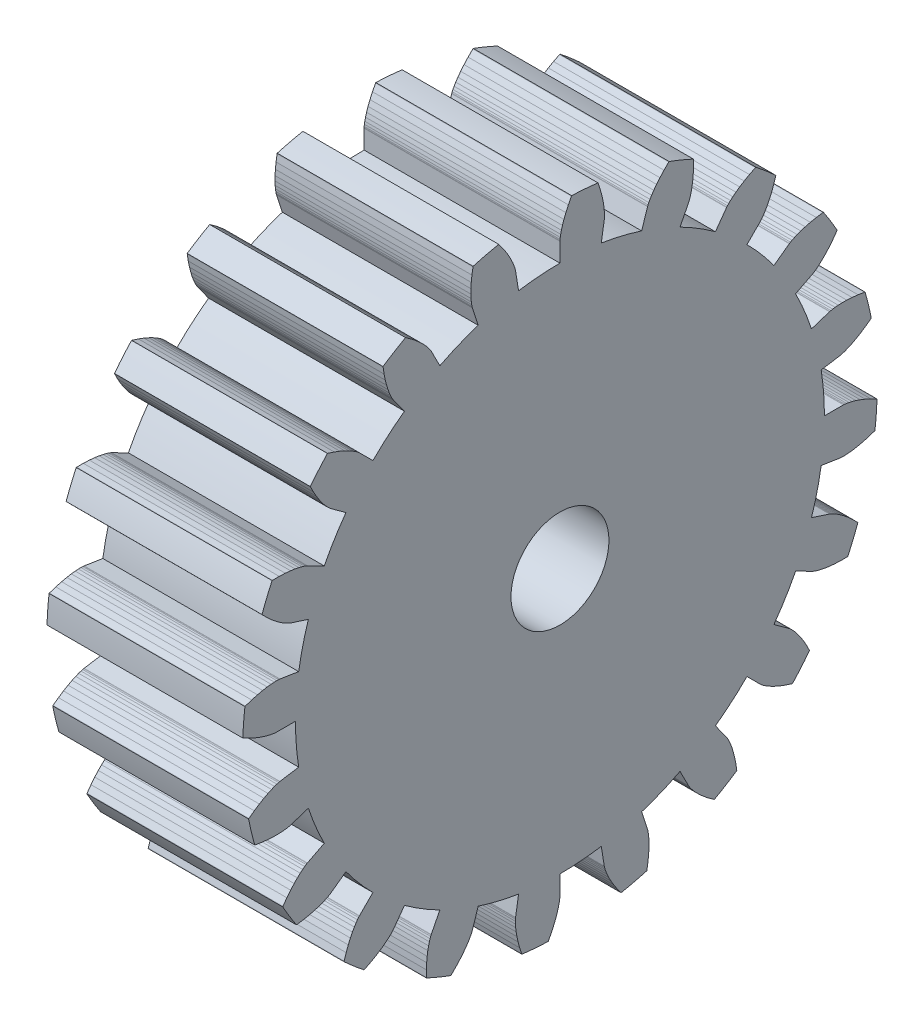
SolidWorks part; units mm, degrees
ref_plane "Front Plane" through (0, 0, 0) normal (0, 0, 1) x (1, 0, 0)
ref_plane "Top Plane" through (0, 0, 0) normal (0, 1, 0) x (1, 0, 0)
ref_plane "Right Plane" through (0, 0, 0) normal (1, 0, 0) x (0, 0, -1)
ref_plane "Plane1" through (12.7, 0, 0) normal (1, 0, 0) x (0, 0, -1)
sketch "Sketch1" plane through (12.7, 0, 0) normal (1, 0, 0) x (0, 0, -1)
  line L0 (2.6828, 16.9386) -> (2.8755, 18.1554)
  line L1 (2.8755, 18.1554) -> (2.8784, 18.1782)
  line L2 (2.8784, 18.1782) -> (2.8838, 18.2469)
  line L3 (2.8838, 18.2469) -> (2.8873, 18.3618)
  line L4 (2.8873, 18.3618) -> (2.8843, 18.5225)
  line L5 (2.8843, 18.5225) -> (2.87, 18.7288)
  line L6 (2.87, 18.7288) -> (2.8401, 18.9798)
  line L7 (2.8401, 18.9798) -> (2.79, 19.2742)
  line L8 (2.79, 19.2742) -> (2.7153, 19.6106)
  line L9 (2.7153, 19.6106) -> (2.6117, 19.9872)
  line L10 (2.6117, 19.9872) -> (2.4751, 20.4018)
  line L11 (2.4751, 20.4018) -> (2.4659, 20.4257)
  line L12 (0.7598, 20.56) -> (0.7469, 20.5378)
  line L13 (0.7469, 20.5378) -> (0.5471, 20.1497)
  line L14 (0.5471, 20.1497) -> (0.3859, 19.794)
  line L15 (0.3859, 19.794) -> (0.2595, 19.4734)
  line L16 (0.2595, 19.4734) -> (0.164, 19.1904)
  line L17 (0.164, 19.1904) -> (0.0951, 18.9472)
  line L18 (0.0951, 18.9472) -> (0.0488, 18.7457)
  line L19 (0.0488, 18.7457) -> (0.0206, 18.5874)
  line L20 (0.0206, 18.5874) -> (0.0061, 18.4734)
  line L21 (0.0061, 18.4734) -> (0.0008, 18.4047)
  line L22 (0.0008, 18.4047) -> (0, 18.3817)
  line L23 (0, 18.3817) -> (0, 17.1498)
  line L24 (-2.6828, 16.9386) -> (-2.8755, 18.1554)
  line L25 (-2.8755, 18.1554) -> (-2.8799, 18.178)
  line L26 (-2.8799, 18.178) -> (-2.8959, 18.245)
  line L27 (-2.8959, 18.245) -> (-2.9281, 18.3553)
  line L28 (-2.9281, 18.3553) -> (-2.9807, 18.5073)
  line L29 (-2.9807, 18.5073) -> (-3.058, 18.6991)
  line L30 (-3.058, 18.6991) -> (-3.164, 18.9285)
  line L31 (-3.164, 18.9285) -> (-3.3026, 19.193)
  line L32 (-3.3026, 19.193) -> (-3.4776, 19.4899)
  line L33 (-3.4776, 19.4899) -> (-3.6925, 19.8161)
  line L34 (-3.6925, 19.8161) -> (-3.9506, 20.1681)
  line L35 (-3.9506, 20.1681) -> (-3.9667, 20.188)
  line L36 (-5.6308, 19.7885) -> (-5.6362, 19.7634)
  line L37 (-5.6362, 19.7634) -> (-5.7063, 19.3326)
  line L38 (-5.7063, 19.3326) -> (-5.7497, 18.9444)
  line L39 (-5.7497, 18.9444) -> (-5.7708, 18.6005)
  line L40 (-5.7708, 18.6005) -> (-5.7742, 18.3018)
  line L41 (-5.7742, 18.3018) -> (-5.7645, 18.0493)
  line L42 (-5.7645, 18.0493) -> (-5.7463, 17.8433)
  line L43 (-5.7463, 17.8433) -> (-5.7242, 17.684)
  line L44 (-5.7242, 17.684) -> (-5.7028, 17.5712)
  line L45 (-5.7028, 17.5712) -> (-5.6866, 17.5041)
  line L46 (-5.6866, 17.5041) -> (-5.6803, 17.4821)
  line L47 (-5.6803, 17.4821) -> (-5.2996, 16.3104)
  line L48 (-7.7858, 15.2806) -> (-8.3451, 16.3782)
  line L49 (-8.3451, 16.3782) -> (-8.3562, 16.3984)
  line L50 (-8.3562, 16.3984) -> (-8.3922, 16.4572)
  line L51 (-8.3922, 16.4572) -> (-8.4569, 16.5521)
  line L52 (-8.4569, 16.5521) -> (-8.5539, 16.6804)
  line L53 (-8.5539, 16.6804) -> (-8.6866, 16.8389)
  line L54 (-8.6866, 16.8389) -> (-8.8583, 17.0243)
  line L55 (-8.8583, 17.0243) -> (-9.0719, 17.2331)
  line L56 (-9.0719, 17.2331) -> (-9.3301, 17.4614)
  line L57 (-9.3301, 17.4614) -> (-9.6353, 17.7051)
  line L58 (-9.6353, 17.7051) -> (-9.9895, 17.9602)
  line L59 (-9.9895, 17.9602) -> (-10.011, 17.9741)
  line L60 (-11.4702, 17.0799) -> (-11.4676, 17.0545)
  line L61 (-11.4676, 17.0545) -> (-11.4011, 16.6231)
  line L62 (-11.4011, 16.6231) -> (-11.3224, 16.2405)
  line L63 (-11.3224, 16.2405) -> (-11.2362, 15.9068)
  line L64 (-11.2362, 15.9068) -> (-11.1472, 15.6217)
  line L65 (-11.1472, 15.6217) -> (-11.0599, 15.3845)
  line L66 (-11.0599, 15.3845) -> (-10.9789, 15.1943)
  line L67 (-10.9789, 15.1943) -> (-10.9087, 15.0496)
  line L68 (-10.9087, 15.0496) -> (-10.8534, 14.9489)
  line L69 (-10.8534, 14.9489) -> (-10.8174, 14.8902)
  line L70 (-10.8174, 14.8902) -> (-10.8045, 14.8711)
  line L71 (-10.8045, 14.8711) -> (-10.0804, 13.8744)
  line L72 (-12.1267, 12.1267) -> (-12.9978, 12.9978)
  line L73 (-12.9978, 12.9978) -> (-13.0146, 13.0135)
  line L74 (-13.0146, 13.0135) -> (-13.067, 13.0583)
  line L75 (-13.067, 13.0583) -> (-13.1578, 13.1287)
  line L76 (-13.1578, 13.1287) -> (-13.2897, 13.2207)
  line L77 (-13.2897, 13.2207) -> (-13.465, 13.3304)
  line L78 (-13.465, 13.3304) -> (-13.6856, 13.4537)
  line L79 (-13.6856, 13.4537) -> (-13.9532, 13.5863)
  line L80 (-13.9532, 13.5863) -> (-14.2693, 13.7236)
  line L81 (-14.2693, 13.7236) -> (-14.6349, 13.8611)
  line L82 (-14.6349, 13.8611) -> (-15.0506, 13.9943)
  line L83 (-15.0506, 13.9943) -> (-15.0753, 14.0009)
  line L84 (-16.1868, 12.6995) -> (-16.1764, 12.6761)
  line L85 (-16.1764, 12.6761) -> (-15.9799, 12.2863)
  line L86 (-15.9799, 12.2863) -> (-15.7868, 11.9468)
  line L87 (-15.7868, 11.9468) -> (-15.6018, 11.6561)
  line L88 (-15.6018, 11.6561) -> (-15.429, 11.4125)
  line L89 (-15.429, 11.4125) -> (-15.2727, 11.2139)
  line L90 (-15.2727, 11.2139) -> (-15.1369, 11.0579)
  line L91 (-15.1369, 11.0579) -> (-15.0254, 10.9421)
  line L92 (-15.0254, 10.9421) -> (-14.9417, 10.8634)
  line L93 (-14.9417, 10.8634) -> (-14.8893, 10.8186)
  line L94 (-14.8893, 10.8186) -> (-14.8711, 10.8045)
  line L95 (-14.8711, 10.8045) -> (-13.8744, 10.0804)
  line L96 (-15.2806, 7.7858) -> (-16.3782, 8.3451)
  line L97 (-16.3782, 8.3451) -> (-16.3991, 8.3549)
  line L98 (-16.3991, 8.3549) -> (-16.4627, 8.3813)
  line L99 (-16.4627, 8.3813) -> (-16.5708, 8.4201)
  line L100 (-16.5708, 8.4201) -> (-16.7247, 8.4669)
  line L101 (-16.7247, 8.4669) -> (-16.9253, 8.5171)
  line L102 (-16.9253, 8.5171) -> (-17.1732, 8.5662)
  line L103 (-17.1732, 8.5662) -> (-17.4687, 8.6095)
  line L104 (-17.4687, 8.6095) -> (-17.8118, 8.6424)
  line L105 (-17.8118, 8.6424) -> (-18.2019, 8.6603)
  line L106 (-18.2019, 8.6603) -> (-18.6384, 8.6585)
  line L107 (-18.6384, 8.6585) -> (-18.664, 8.6571)
  line L108 (-19.3189, 7.076) -> (-19.3018, 7.0569)
  line L109 (-19.3018, 7.0569) -> (-18.9945, 6.7469)
  line L110 (-18.9945, 6.7469) -> (-18.7059, 6.4837)
  line L111 (-18.7059, 6.4837) -> (-18.4401, 6.2644)
  line L112 (-18.4401, 6.2644) -> (-18.2005, 6.0861)
  line L113 (-18.2005, 6.0861) -> (-17.9905, 5.9455)
  line L114 (-17.9905, 5.9455) -> (-17.8131, 5.8392)
  line L115 (-17.8131, 5.8392) -> (-17.6713, 5.7634)
  line L116 (-17.6713, 5.7634) -> (-17.5674, 5.7144)
  line L117 (-17.5674, 5.7144) -> (-17.5037, 5.6881)
  line L118 (-17.5037, 5.6881) -> (-17.4821, 5.6803)
  line L119 (-17.4821, 5.6803) -> (-16.3104, 5.2996)
  line L120 (-16.9386, 2.6828) -> (-18.1554, 2.8755)
  line L121 (-18.1554, 2.8755) -> (-18.1782, 2.8784)
  line L122 (-18.1782, 2.8784) -> (-18.2469, 2.8838)
  line L123 (-18.2469, 2.8838) -> (-18.3618, 2.8873)
  line L124 (-18.3618, 2.8873) -> (-18.5225, 2.8843)
  line L125 (-18.5225, 2.8843) -> (-18.7288, 2.87)
  line L126 (-18.7288, 2.87) -> (-18.9798, 2.8401)
  line L127 (-18.9798, 2.8401) -> (-19.2742, 2.79)
  line L128 (-19.2742, 2.79) -> (-19.6106, 2.7153)
  line L129 (-19.6106, 2.7153) -> (-19.9872, 2.6117)
  line L130 (-19.9872, 2.6117) -> (-20.4018, 2.4751)
  line L131 (-20.4018, 2.4751) -> (-20.4257, 2.4659)
  line L132 (-20.56, 0.7598) -> (-20.5378, 0.7469)
  line L133 (-20.5378, 0.7469) -> (-20.1497, 0.5471)
  line L134 (-20.1497, 0.5471) -> (-19.794, 0.3859)
  line L135 (-19.794, 0.3859) -> (-19.4734, 0.2595)
  line L136 (-19.4734, 0.2595) -> (-19.1904, 0.164)
  line L137 (-19.1904, 0.164) -> (-18.9472, 0.0951)
  line L138 (-18.9472, 0.0951) -> (-18.7457, 0.0488)
  line L139 (-18.7457, 0.0488) -> (-18.5874, 0.0206)
  line L140 (-18.5874, 0.0206) -> (-18.4734, 0.0061)
  line L141 (-18.4734, 0.0061) -> (-18.4047, 0.0008)
  line L142 (-18.4047, 0.0008) -> (-18.3817, 0)
  line L143 (-18.3817, 0) -> (-17.1498, 0)
  line L144 (-16.9386, -2.6828) -> (-18.1554, -2.8755)
  line L145 (-18.1554, -2.8755) -> (-18.178, -2.8799)
  line L146 (-18.178, -2.8799) -> (-18.245, -2.8959)
  line L147 (-18.245, -2.8959) -> (-18.3553, -2.9281)
  line L148 (-18.3553, -2.9281) -> (-18.5073, -2.9807)
  line L149 (-18.5073, -2.9807) -> (-18.6991, -3.058)
  line L150 (-18.6991, -3.058) -> (-18.9285, -3.164)
  line L151 (-18.9285, -3.164) -> (-19.193, -3.3026)
  line L152 (-19.193, -3.3026) -> (-19.4899, -3.4776)
  line L153 (-19.4899, -3.4776) -> (-19.8161, -3.6925)
  line L154 (-19.8161, -3.6925) -> (-20.1681, -3.9506)
  line L155 (-20.1681, -3.9506) -> (-20.188, -3.9667)
  line L156 (-19.7885, -5.6308) -> (-19.7634, -5.6362)
  line L157 (-19.7634, -5.6362) -> (-19.3326, -5.7063)
  line L158 (-19.3326, -5.7063) -> (-18.9444, -5.7497)
  line L159 (-18.9444, -5.7497) -> (-18.6005, -5.7708)
  line L160 (-18.6005, -5.7708) -> (-18.3018, -5.7742)
  line L161 (-18.3018, -5.7742) -> (-18.0493, -5.7645)
  line L162 (-18.0493, -5.7645) -> (-17.8433, -5.7463)
  line L163 (-17.8433, -5.7463) -> (-17.684, -5.7242)
  line L164 (-17.684, -5.7242) -> (-17.5712, -5.7028)
  line L165 (-17.5712, -5.7028) -> (-17.5041, -5.6866)
  line L166 (-17.5041, -5.6866) -> (-17.4821, -5.6803)
  line L167 (-17.4821, -5.6803) -> (-16.3104, -5.2996)
  line L168 (-15.2806, -7.7858) -> (-16.3782, -8.3451)
  line L169 (-16.3782, -8.3451) -> (-16.3984, -8.3562)
  line L170 (-16.3984, -8.3562) -> (-16.4572, -8.3922)
  line L171 (-16.4572, -8.3922) -> (-16.5521, -8.4569)
  line L172 (-16.5521, -8.4569) -> (-16.6804, -8.5539)
  line L173 (-16.6804, -8.5539) -> (-16.8389, -8.6866)
  line L174 (-16.8389, -8.6866) -> (-17.0243, -8.8583)
  line L175 (-17.0243, -8.8583) -> (-17.2331, -9.0719)
  line L176 (-17.2331, -9.0719) -> (-17.4614, -9.3301)
  line L177 (-17.4614, -9.3301) -> (-17.7051, -9.6353)
  line L178 (-17.7051, -9.6353) -> (-17.9602, -9.9895)
  line L179 (-17.9602, -9.9895) -> (-17.9741, -10.011)
  line L180 (-17.0799, -11.4702) -> (-17.0545, -11.4676)
  line L181 (-17.0545, -11.4676) -> (-16.6231, -11.4011)
  line L182 (-16.6231, -11.4011) -> (-16.2405, -11.3224)
  line L183 (-16.2405, -11.3224) -> (-15.9068, -11.2362)
  line L184 (-15.9068, -11.2362) -> (-15.6217, -11.1472)
  line L185 (-15.6217, -11.1472) -> (-15.3845, -11.0599)
  line L186 (-15.3845, -11.0599) -> (-15.1943, -10.9789)
  line L187 (-15.1943, -10.9789) -> (-15.0496, -10.9087)
  line L188 (-15.0496, -10.9087) -> (-14.9489, -10.8534)
  line L189 (-14.9489, -10.8534) -> (-14.8902, -10.8174)
  line L190 (-14.8902, -10.8174) -> (-14.8711, -10.8045)
  line L191 (-14.8711, -10.8045) -> (-13.8744, -10.0804)
  line L192 (-12.1267, -12.1267) -> (-12.9978, -12.9978)
  line L193 (-12.9978, -12.9978) -> (-13.0135, -13.0146)
  line L194 (-13.0135, -13.0146) -> (-13.0583, -13.067)
  line L195 (-13.0583, -13.067) -> (-13.1287, -13.1578)
  line L196 (-13.1287, -13.1578) -> (-13.2207, -13.2897)
  line L197 (-13.2207, -13.2897) -> (-13.3304, -13.465)
  line L198 (-13.3304, -13.465) -> (-13.4537, -13.6856)
  line L199 (-13.4537, -13.6856) -> (-13.5863, -13.9532)
  line L200 (-13.5863, -13.9532) -> (-13.7236, -14.2693)
  line L201 (-13.7236, -14.2693) -> (-13.8611, -14.6349)
  line L202 (-13.8611, -14.6349) -> (-13.9943, -15.0506)
  line L203 (-13.9943, -15.0506) -> (-14.0009, -15.0753)
  line L204 (-12.6995, -16.1868) -> (-12.6761, -16.1764)
  line L205 (-12.6761, -16.1764) -> (-12.2863, -15.9799)
  line L206 (-12.2863, -15.9799) -> (-11.9468, -15.7868)
  line L207 (-11.9468, -15.7868) -> (-11.6561, -15.6018)
  line L208 (-11.6561, -15.6018) -> (-11.4125, -15.429)
  line L209 (-11.4125, -15.429) -> (-11.2139, -15.2727)
  line L210 (-11.2139, -15.2727) -> (-11.0579, -15.1369)
  line L211 (-11.0579, -15.1369) -> (-10.9421, -15.0254)
  line L212 (-10.9421, -15.0254) -> (-10.8634, -14.9417)
  line L213 (-10.8634, -14.9417) -> (-10.8186, -14.8893)
  line L214 (-10.8186, -14.8893) -> (-10.8045, -14.8711)
  line L215 (-10.8045, -14.8711) -> (-10.0804, -13.8744)
  line L216 (-7.7858, -15.2806) -> (-8.3451, -16.3782)
  line L217 (-8.3451, -16.3782) -> (-8.3549, -16.3991)
  line L218 (-8.3549, -16.3991) -> (-8.3813, -16.4627)
  line L219 (-8.3813, -16.4627) -> (-8.4201, -16.5708)
  line L220 (-8.4201, -16.5708) -> (-8.4669, -16.7247)
  line L221 (-8.4669, -16.7247) -> (-8.5171, -16.9253)
  line L222 (-8.5171, -16.9253) -> (-8.5662, -17.1732)
  line L223 (-8.5662, -17.1732) -> (-8.6095, -17.4687)
  line L224 (-8.6095, -17.4687) -> (-8.6424, -17.8118)
  line L225 (-8.6424, -17.8118) -> (-8.6603, -18.2019)
  line L226 (-8.6603, -18.2019) -> (-8.6585, -18.6384)
  line L227 (-8.6585, -18.6384) -> (-8.6571, -18.664)
  line L228 (-7.076, -19.3189) -> (-7.0569, -19.3018)
  line L229 (-7.0569, -19.3018) -> (-6.7469, -18.9945)
  line L230 (-6.7469, -18.9945) -> (-6.4837, -18.7059)
  line L231 (-6.4837, -18.7059) -> (-6.2644, -18.4401)
  line L232 (-6.2644, -18.4401) -> (-6.0861, -18.2005)
  line L233 (-6.0861, -18.2005) -> (-5.9455, -17.9905)
  line L234 (-5.9455, -17.9905) -> (-5.8392, -17.8131)
  line L235 (-5.8392, -17.8131) -> (-5.7634, -17.6713)
  line L236 (-5.7634, -17.6713) -> (-5.7144, -17.5674)
  line L237 (-5.7144, -17.5674) -> (-5.6881, -17.5037)
  line L238 (-5.6881, -17.5037) -> (-5.6803, -17.4821)
  line L239 (-5.6803, -17.4821) -> (-5.2996, -16.3104)
  line L240 (-2.6828, -16.9386) -> (-2.8755, -18.1554)
  line L241 (-2.8755, -18.1554) -> (-2.8784, -18.1782)
  line L242 (-2.8784, -18.1782) -> (-2.8838, -18.2469)
  line L243 (-2.8838, -18.2469) -> (-2.8873, -18.3618)
  line L244 (-2.8873, -18.3618) -> (-2.8843, -18.5225)
  line L245 (-2.8843, -18.5225) -> (-2.87, -18.7288)
  line L246 (-2.87, -18.7288) -> (-2.8401, -18.9798)
  line L247 (-2.8401, -18.9798) -> (-2.79, -19.2742)
  line L248 (-2.79, -19.2742) -> (-2.7153, -19.6106)
  line L249 (-2.7153, -19.6106) -> (-2.6117, -19.9872)
  line L250 (-2.6117, -19.9872) -> (-2.4751, -20.4018)
  line L251 (-2.4751, -20.4018) -> (-2.4659, -20.4257)
  line L252 (-0.7598, -20.56) -> (-0.7469, -20.5378)
  line L253 (-0.7469, -20.5378) -> (-0.5471, -20.1497)
  line L254 (-0.5471, -20.1497) -> (-0.3859, -19.794)
  line L255 (-0.3859, -19.794) -> (-0.2595, -19.4734)
  line L256 (-0.2595, -19.4734) -> (-0.164, -19.1904)
  line L257 (-0.164, -19.1904) -> (-0.0951, -18.9472)
  line L258 (-0.0951, -18.9472) -> (-0.0488, -18.7457)
  line L259 (-0.0488, -18.7457) -> (-0.0206, -18.5874)
  line L260 (-0.0206, -18.5874) -> (-0.0061, -18.4734)
  line L261 (-0.0061, -18.4734) -> (-0.0008, -18.4047)
  line L262 (-0.0008, -18.4047) -> (0, -18.3817)
  line L263 (0, -18.3817) -> (0, -17.1498)
  line L264 (2.6828, -16.9386) -> (2.8755, -18.1554)
  line L265 (2.8755, -18.1554) -> (2.8799, -18.178)
  line L266 (2.8799, -18.178) -> (2.8959, -18.245)
  line L267 (2.8959, -18.245) -> (2.9281, -18.3553)
  line L268 (2.9281, -18.3553) -> (2.9807, -18.5073)
  line L269 (2.9807, -18.5073) -> (3.058, -18.6991)
  line L270 (3.058, -18.6991) -> (3.164, -18.9285)
  line L271 (3.164, -18.9285) -> (3.3026, -19.193)
  line L272 (3.3026, -19.193) -> (3.4776, -19.4899)
  line L273 (3.4776, -19.4899) -> (3.6925, -19.8161)
  line L274 (3.6925, -19.8161) -> (3.9506, -20.1681)
  line L275 (3.9506, -20.1681) -> (3.9667, -20.188)
  line L276 (5.6308, -19.7885) -> (5.6362, -19.7634)
  line L277 (5.6362, -19.7634) -> (5.7063, -19.3326)
  line L278 (5.7063, -19.3326) -> (5.7497, -18.9444)
  line L279 (5.7497, -18.9444) -> (5.7708, -18.6005)
  line L280 (5.7708, -18.6005) -> (5.7742, -18.3018)
  line L281 (5.7742, -18.3018) -> (5.7645, -18.0493)
  line L282 (5.7645, -18.0493) -> (5.7463, -17.8433)
  line L283 (5.7463, -17.8433) -> (5.7242, -17.684)
  line L284 (5.7242, -17.684) -> (5.7028, -17.5712)
  line L285 (5.7028, -17.5712) -> (5.6866, -17.5041)
  line L286 (5.6866, -17.5041) -> (5.6803, -17.4821)
  line L287 (5.6803, -17.4821) -> (5.2996, -16.3104)
  line L288 (7.7858, -15.2806) -> (8.3451, -16.3782)
  line L289 (8.3451, -16.3782) -> (8.3562, -16.3984)
  line L290 (8.3562, -16.3984) -> (8.3922, -16.4572)
  line L291 (8.3922, -16.4572) -> (8.4569, -16.5521)
  line L292 (8.4569, -16.5521) -> (8.5539, -16.6804)
  line L293 (8.5539, -16.6804) -> (8.6866, -16.8389)
  line L294 (8.6866, -16.8389) -> (8.8583, -17.0243)
  line L295 (8.8583, -17.0243) -> (9.0719, -17.2331)
  line L296 (9.0719, -17.2331) -> (9.3301, -17.4614)
  line L297 (9.3301, -17.4614) -> (9.6353, -17.7051)
  line L298 (9.6353, -17.7051) -> (9.9895, -17.9602)
  line L299 (9.9895, -17.9602) -> (10.011, -17.9741)
  line L300 (11.4702, -17.0799) -> (11.4676, -17.0545)
  line L301 (11.4676, -17.0545) -> (11.4011, -16.6231)
  line L302 (11.4011, -16.6231) -> (11.3224, -16.2405)
  line L303 (11.3224, -16.2405) -> (11.2362, -15.9068)
  line L304 (11.2362, -15.9068) -> (11.1472, -15.6217)
  line L305 (11.1472, -15.6217) -> (11.0599, -15.3845)
  line L306 (11.0599, -15.3845) -> (10.9789, -15.1943)
  line L307 (10.9789, -15.1943) -> (10.9087, -15.0496)
  line L308 (10.9087, -15.0496) -> (10.8534, -14.9489)
  line L309 (10.8534, -14.9489) -> (10.8174, -14.8902)
  line L310 (10.8174, -14.8902) -> (10.8045, -14.8711)
  line L311 (10.8045, -14.8711) -> (10.0804, -13.8744)
  line L312 (12.1267, -12.1267) -> (12.9978, -12.9978)
  line L313 (12.9978, -12.9978) -> (13.0146, -13.0135)
  line L314 (13.0146, -13.0135) -> (13.067, -13.0583)
  line L315 (13.067, -13.0583) -> (13.1578, -13.1287)
  line L316 (13.1578, -13.1287) -> (13.2897, -13.2207)
  line L317 (13.2897, -13.2207) -> (13.465, -13.3304)
  line L318 (13.465, -13.3304) -> (13.6856, -13.4537)
  line L319 (13.6856, -13.4537) -> (13.9532, -13.5863)
  line L320 (13.9532, -13.5863) -> (14.2693, -13.7236)
  line L321 (14.2693, -13.7236) -> (14.6349, -13.8611)
  line L322 (14.6349, -13.8611) -> (15.0506, -13.9943)
  line L323 (15.0506, -13.9943) -> (15.0753, -14.0009)
  line L324 (16.1868, -12.6995) -> (16.1764, -12.6761)
  line L325 (16.1764, -12.6761) -> (15.9799, -12.2863)
  line L326 (15.9799, -12.2863) -> (15.7868, -11.9468)
  line L327 (15.7868, -11.9468) -> (15.6018, -11.6561)
  line L328 (15.6018, -11.6561) -> (15.429, -11.4125)
  line L329 (15.429, -11.4125) -> (15.2727, -11.2139)
  line L330 (15.2727, -11.2139) -> (15.1369, -11.0579)
  line L331 (15.1369, -11.0579) -> (15.0254, -10.9421)
  line L332 (15.0254, -10.9421) -> (14.9417, -10.8634)
  line L333 (14.9417, -10.8634) -> (14.8893, -10.8186)
  line L334 (14.8893, -10.8186) -> (14.8711, -10.8045)
  line L335 (14.8711, -10.8045) -> (13.8744, -10.0804)
  line L336 (15.2806, -7.7858) -> (16.3782, -8.3451)
  line L337 (16.3782, -8.3451) -> (16.3991, -8.3549)
  line L338 (16.3991, -8.3549) -> (16.4627, -8.3813)
  line L339 (16.4627, -8.3813) -> (16.5708, -8.4201)
  line L340 (16.5708, -8.4201) -> (16.7247, -8.4669)
  line L341 (16.7247, -8.4669) -> (16.9253, -8.5171)
  line L342 (16.9253, -8.5171) -> (17.1732, -8.5662)
  line L343 (17.1732, -8.5662) -> (17.4687, -8.6095)
  line L344 (17.4687, -8.6095) -> (17.8118, -8.6424)
  line L345 (17.8118, -8.6424) -> (18.2019, -8.6603)
  line L346 (18.2019, -8.6603) -> (18.6384, -8.6585)
  line L347 (18.6384, -8.6585) -> (18.664, -8.6571)
  line L348 (19.3189, -7.076) -> (19.3018, -7.0569)
  line L349 (19.3018, -7.0569) -> (18.9945, -6.7469)
  line L350 (18.9945, -6.7469) -> (18.7059, -6.4837)
  line L351 (18.7059, -6.4837) -> (18.4401, -6.2644)
  line L352 (18.4401, -6.2644) -> (18.2005, -6.0861)
  line L353 (18.2005, -6.0861) -> (17.9905, -5.9455)
  line L354 (17.9905, -5.9455) -> (17.8131, -5.8392)
  line L355 (17.8131, -5.8392) -> (17.6713, -5.7634)
  line L356 (17.6713, -5.7634) -> (17.5674, -5.7144)
  line L357 (17.5674, -5.7144) -> (17.5037, -5.6881)
  line L358 (17.5037, -5.6881) -> (17.4821, -5.6803)
  line L359 (17.4821, -5.6803) -> (16.3104, -5.2996)
  line L360 (16.9386, -2.6828) -> (18.1554, -2.8755)
  line L361 (18.1554, -2.8755) -> (18.1782, -2.8784)
  line L362 (18.1782, -2.8784) -> (18.2469, -2.8838)
  line L363 (18.2469, -2.8838) -> (18.3618, -2.8873)
  line L364 (18.3618, -2.8873) -> (18.5225, -2.8843)
  line L365 (18.5225, -2.8843) -> (18.7288, -2.87)
  line L366 (18.7288, -2.87) -> (18.9798, -2.8401)
  line L367 (18.9798, -2.8401) -> (19.2742, -2.79)
  line L368 (19.2742, -2.79) -> (19.6106, -2.7153)
  line L369 (19.6106, -2.7153) -> (19.9872, -2.6117)
  line L370 (19.9872, -2.6117) -> (20.4018, -2.4751)
  line L371 (20.4018, -2.4751) -> (20.4257, -2.4659)
  line L372 (20.56, -0.7598) -> (20.5378, -0.7469)
  line L373 (20.5378, -0.7469) -> (20.1497, -0.5471)
  line L374 (20.1497, -0.5471) -> (19.794, -0.3859)
  line L375 (19.794, -0.3859) -> (19.4734, -0.2595)
  line L376 (19.4734, -0.2595) -> (19.1904, -0.164)
  line L377 (19.1904, -0.164) -> (18.9472, -0.0951)
  line L378 (18.9472, -0.0951) -> (18.7457, -0.0488)
  line L379 (18.7457, -0.0488) -> (18.5874, -0.0206)
  line L380 (18.5874, -0.0206) -> (18.4734, -0.0061)
  line L381 (18.4734, -0.0061) -> (18.4047, -0.0008)
  line L382 (18.4047, -0.0008) -> (18.3817, 0)
  line L383 (18.3817, 0) -> (17.1498, 0)
  line L384 (16.9386, 2.6828) -> (18.1554, 2.8755)
  line L385 (18.1554, 2.8755) -> (18.178, 2.8799)
  line L386 (18.178, 2.8799) -> (18.245, 2.8959)
  line L387 (18.245, 2.8959) -> (18.3553, 2.9281)
  line L388 (18.3553, 2.9281) -> (18.5073, 2.9807)
  line L389 (18.5073, 2.9807) -> (18.6991, 3.058)
  line L390 (18.6991, 3.058) -> (18.9285, 3.164)
  line L391 (18.9285, 3.164) -> (19.193, 3.3026)
  line L392 (19.193, 3.3026) -> (19.4899, 3.4776)
  line L393 (19.4899, 3.4776) -> (19.8161, 3.6925)
  line L394 (19.8161, 3.6925) -> (20.1681, 3.9506)
  line L395 (20.1681, 3.9506) -> (20.188, 3.9667)
  line L396 (19.7885, 5.6308) -> (19.7634, 5.6362)
  line L397 (19.7634, 5.6362) -> (19.3326, 5.7063)
  line L398 (19.3326, 5.7063) -> (18.9444, 5.7497)
  line L399 (18.9444, 5.7497) -> (18.6005, 5.7708)
  line L400 (18.6005, 5.7708) -> (18.3018, 5.7742)
  line L401 (18.3018, 5.7742) -> (18.0493, 5.7645)
  line L402 (18.0493, 5.7645) -> (17.8433, 5.7463)
  line L403 (17.8433, 5.7463) -> (17.684, 5.7242)
  line L404 (17.684, 5.7242) -> (17.5712, 5.7028)
  line L405 (17.5712, 5.7028) -> (17.5041, 5.6866)
  line L406 (17.5041, 5.6866) -> (17.4821, 5.6803)
  line L407 (17.4821, 5.6803) -> (16.3104, 5.2996)
  line L408 (15.2806, 7.7858) -> (16.3782, 8.3451)
  line L409 (16.3782, 8.3451) -> (16.3984, 8.3562)
  line L410 (16.3984, 8.3562) -> (16.4572, 8.3922)
  line L411 (16.4572, 8.3922) -> (16.5521, 8.4569)
  line L412 (16.5521, 8.4569) -> (16.6804, 8.5539)
  line L413 (16.6804, 8.5539) -> (16.8389, 8.6866)
  line L414 (16.8389, 8.6866) -> (17.0243, 8.8583)
  line L415 (17.0243, 8.8583) -> (17.2331, 9.0719)
  line L416 (17.2331, 9.0719) -> (17.4614, 9.3301)
  line L417 (17.4614, 9.3301) -> (17.7051, 9.6353)
  line L418 (17.7051, 9.6353) -> (17.9602, 9.9895)
  line L419 (17.9602, 9.9895) -> (17.9741, 10.011)
  line L420 (17.0799, 11.4702) -> (17.0545, 11.4676)
  line L421 (17.0545, 11.4676) -> (16.6231, 11.4011)
  line L422 (16.6231, 11.4011) -> (16.2405, 11.3224)
  line L423 (16.2405, 11.3224) -> (15.9068, 11.2362)
  line L424 (15.9068, 11.2362) -> (15.6217, 11.1472)
  line L425 (15.6217, 11.1472) -> (15.3845, 11.0599)
  line L426 (15.3845, 11.0599) -> (15.1943, 10.9789)
  line L427 (15.1943, 10.9789) -> (15.0496, 10.9087)
  line L428 (15.0496, 10.9087) -> (14.9489, 10.8534)
  line L429 (14.9489, 10.8534) -> (14.8902, 10.8174)
  line L430 (14.8902, 10.8174) -> (14.8711, 10.8045)
  line L431 (14.8711, 10.8045) -> (13.8744, 10.0804)
  line L432 (12.1267, 12.1267) -> (12.9978, 12.9978)
  line L433 (12.9978, 12.9978) -> (13.0135, 13.0146)
  line L434 (13.0135, 13.0146) -> (13.0583, 13.067)
  line L435 (13.0583, 13.067) -> (13.1287, 13.1578)
  line L436 (13.1287, 13.1578) -> (13.2207, 13.2897)
  line L437 (13.2207, 13.2897) -> (13.3304, 13.465)
  line L438 (13.3304, 13.465) -> (13.4537, 13.6856)
  line L439 (13.4537, 13.6856) -> (13.5863, 13.9532)
  line L440 (13.5863, 13.9532) -> (13.7236, 14.2693)
  line L441 (13.7236, 14.2693) -> (13.8611, 14.6349)
  line L442 (13.8611, 14.6349) -> (13.9943, 15.0506)
  line L443 (13.9943, 15.0506) -> (14.0009, 15.0753)
  line L444 (12.6995, 16.1868) -> (12.6761, 16.1764)
  line L445 (12.6761, 16.1764) -> (12.2863, 15.9799)
  line L446 (12.2863, 15.9799) -> (11.9468, 15.7868)
  line L447 (11.9468, 15.7868) -> (11.6561, 15.6018)
  line L448 (11.6561, 15.6018) -> (11.4125, 15.429)
  line L449 (11.4125, 15.429) -> (11.2139, 15.2727)
  line L450 (11.2139, 15.2727) -> (11.0579, 15.1369)
  line L451 (11.0579, 15.1369) -> (10.9421, 15.0254)
  line L452 (10.9421, 15.0254) -> (10.8634, 14.9417)
  line L453 (10.8634, 14.9417) -> (10.8186, 14.8893)
  line L454 (10.8186, 14.8893) -> (10.8045, 14.8711)
  line L455 (10.8045, 14.8711) -> (10.0804, 13.8744)
  line L456 (7.7858, 15.2806) -> (8.3451, 16.3782)
  line L457 (8.3451, 16.3782) -> (8.3549, 16.3991)
  line L458 (8.3549, 16.3991) -> (8.3813, 16.4627)
  line L459 (8.3813, 16.4627) -> (8.4201, 16.5708)
  line L460 (8.4201, 16.5708) -> (8.4669, 16.7247)
  line L461 (8.4669, 16.7247) -> (8.5171, 16.9253)
  line L462 (8.5171, 16.9253) -> (8.5662, 17.1732)
  line L463 (8.5662, 17.1732) -> (8.6095, 17.4687)
  line L464 (8.6095, 17.4687) -> (8.6424, 17.8118)
  line L465 (8.6424, 17.8118) -> (8.6603, 18.2019)
  line L466 (8.6603, 18.2019) -> (8.6585, 18.6384)
  line L467 (8.6585, 18.6384) -> (8.6571, 18.664)
  line L468 (7.076, 19.3189) -> (7.0569, 19.3018)
  line L469 (7.0569, 19.3018) -> (6.7469, 18.9945)
  line L470 (6.7469, 18.9945) -> (6.4837, 18.7059)
  line L471 (6.4837, 18.7059) -> (6.2644, 18.4401)
  line L472 (6.2644, 18.4401) -> (6.0861, 18.2005)
  line L473 (6.0861, 18.2005) -> (5.9455, 17.9905)
  line L474 (5.9455, 17.9905) -> (5.8392, 17.8131)
  line L475 (5.8392, 17.8131) -> (5.7634, 17.6713)
  line L476 (5.7634, 17.6713) -> (5.7144, 17.5674)
  line L477 (5.7144, 17.5674) -> (5.6881, 17.5037)
  line L478 (5.6881, 17.5037) -> (5.6803, 17.4821)
  line L479 (5.6803, 17.4821) -> (5.2996, 16.3104)
  arc A0 (5.2996, 16.3104) -> (2.6828, 16.9386) centre (0, 0) ccw
  arc A1 (2.4659, 20.4257) -> (0.7598, 20.56) centre (0, 0) ccw
  arc A2 (0, 17.1498) -> (-2.6828, 16.9386) centre (0, 0) ccw
  arc A3 (-3.9667, 20.188) -> (-5.6308, 19.7885) centre (0, 0) ccw
  arc A4 (-5.2996, 16.3104) -> (-7.7858, 15.2806) centre (0, 0) ccw
  arc A5 (-10.011, 17.9741) -> (-11.4702, 17.0799) centre (0, 0) ccw
  arc A6 (-10.0804, 13.8744) -> (-12.1267, 12.1267) centre (0, 0) ccw
  arc A7 (-15.0753, 14.0009) -> (-16.1868, 12.6995) centre (0, 0) ccw
  arc A8 (-13.8744, 10.0804) -> (-15.2806, 7.7858) centre (0, 0) ccw
  arc A9 (-18.664, 8.6571) -> (-19.3189, 7.076) centre (0, 0) ccw
  arc A10 (-16.3104, 5.2996) -> (-16.9386, 2.6828) centre (0, 0) ccw
  arc A11 (-20.4257, 2.4659) -> (-20.56, 0.7598) centre (0, 0) ccw
  arc A12 (-17.1498, 0) -> (-16.9386, -2.6828) centre (0, 0) ccw
  arc A13 (-20.188, -3.9667) -> (-19.7885, -5.6308) centre (0, 0) ccw
  arc A14 (-16.3104, -5.2996) -> (-15.2806, -7.7858) centre (0, 0) ccw
  arc A15 (-17.9741, -10.011) -> (-17.0799, -11.4702) centre (0, 0) ccw
  arc A16 (-13.8744, -10.0804) -> (-12.1267, -12.1267) centre (0, 0) ccw
  arc A17 (-14.0009, -15.0753) -> (-12.6995, -16.1868) centre (0, 0) ccw
  arc A18 (-10.0804, -13.8744) -> (-7.7858, -15.2806) centre (0, 0) ccw
  arc A19 (-8.6571, -18.664) -> (-7.076, -19.3189) centre (0, 0) ccw
  arc A20 (-5.2996, -16.3104) -> (-2.6828, -16.9386) centre (0, 0) ccw
  arc A21 (-2.4659, -20.4257) -> (-0.7598, -20.56) centre (0, 0) ccw
  arc A22 (0, -17.1498) -> (2.6828, -16.9386) centre (0, 0) ccw
  arc A23 (3.9667, -20.188) -> (5.6308, -19.7885) centre (0, 0) ccw
  arc A24 (5.2996, -16.3104) -> (7.7858, -15.2806) centre (0, 0) ccw
  arc A25 (10.011, -17.9741) -> (11.4702, -17.0799) centre (0, 0) ccw
  arc A26 (10.0804, -13.8744) -> (12.1267, -12.1267) centre (0, 0) ccw
  arc A27 (15.0753, -14.0009) -> (16.1868, -12.6995) centre (0, 0) ccw
  arc A28 (13.8744, -10.0804) -> (15.2806, -7.7858) centre (0, 0) ccw
  arc A29 (18.664, -8.6571) -> (19.3189, -7.076) centre (0, 0) ccw
  arc A30 (16.3104, -5.2996) -> (16.9386, -2.6828) centre (0, 0) ccw
  arc A31 (20.4257, -2.4659) -> (20.56, -0.7598) centre (0, 0) ccw
  arc A32 (17.1498, 0) -> (16.9386, 2.6828) centre (0, 0) ccw
  arc A33 (20.188, 3.9667) -> (19.7885, 5.6308) centre (0, 0) ccw
  arc A34 (16.3104, 5.2996) -> (15.2806, 7.7858) centre (0, 0) ccw
  arc A35 (17.9741, 10.011) -> (17.0799, 11.4702) centre (0, 0) ccw
  arc A36 (13.8744, 10.0804) -> (12.1267, 12.1267) centre (0, 0) ccw
  arc A37 (14.0009, 15.0753) -> (12.6995, 16.1868) centre (0, 0) ccw
  arc A38 (10.0804, 13.8744) -> (7.7858, 15.2806) centre (0, 0) ccw
  arc A39 (8.6571, 18.664) -> (7.076, 19.3189) centre (0, 0) ccw
extrude "Boss-Extrude1" add sketch "Sketch1" against normal blind 12.7
sketch "Sketch2" plane through (0, 0, 0) normal (-1, 0, 0) x (0, 0, 1)
  circle A0 centre (0, 0) radius 3.175
  dimension "D1" = 6.35
extrude "Cut-Extrude1" cut sketch "Sketch2" against normal through all
